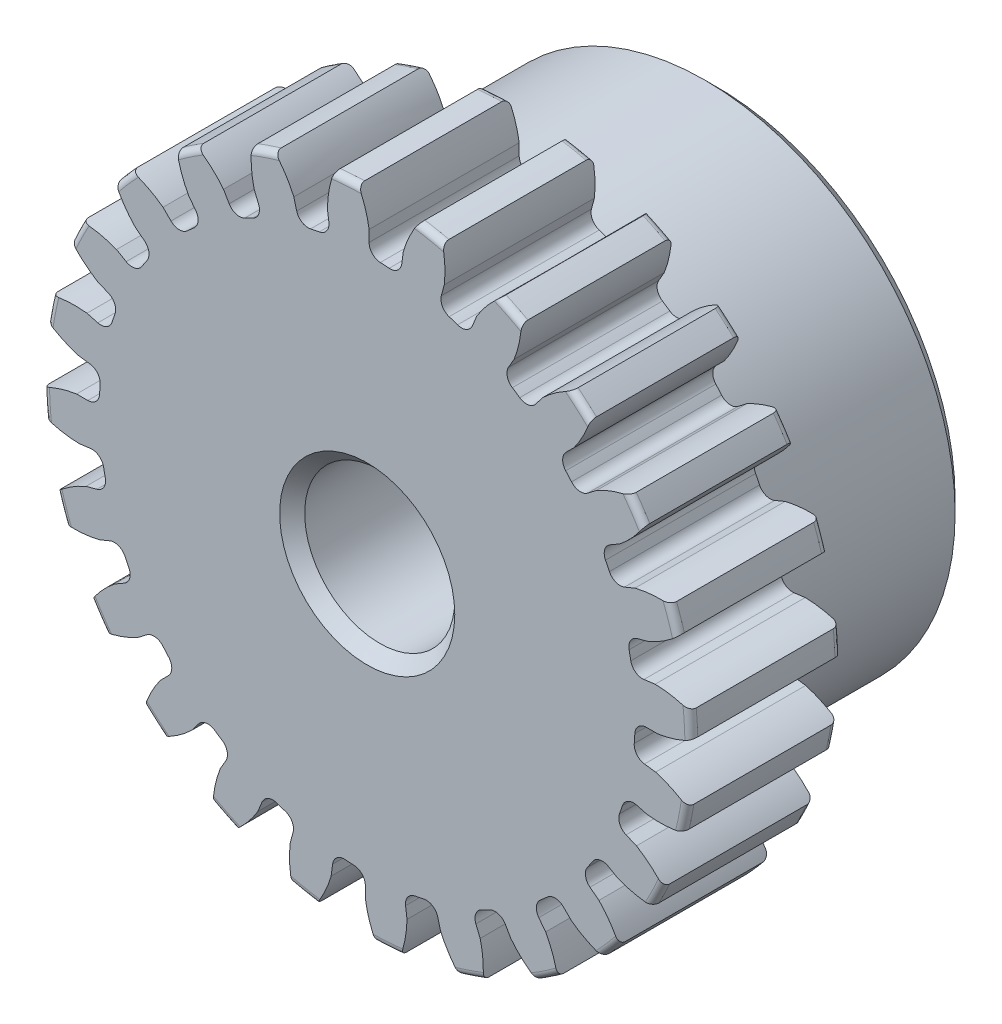
SolidWorks part; units mm, degrees
ref_plane "Front" through (0, 0, 0) normal (0, 0, 1) x (1, 0, 0)
ref_plane "Top" through (0, 0, 0) normal (0, 1, 0) x (1, 0, 0)
ref_plane "Right" through (0, 0, 0) normal (1, 0, 0) x (0, 0, -1)
sketch "Sketch1" plane through (0, 0, 0) normal (0, 0, 1) x (1, 0, 0)
  line L0 (-304.8, 0) -> (304.8, 0) construction
  circle A0 centre (0, 0) radius 10.287
  circle A1 centre (0, 0) radius 9.525 construction
  circle A3 centre (0, 0) radius 8.5011 construction
  dimension "D1" = 1.7859
  dimension "OD" = 20.574
  dimension "Ptich Dia" = 19.05
  dimension "Root Dia" = 17.0021
  dimension "D3" = 0.762
  dimension "Number of Teeth" = 609.6
extrude "Boss-Extrude1" add sketch "Sketch1" against normal blind 4.7625
sketch "Sketch2" plane through (0, 0, 0) normal (1, 0, 0) x (0, 0, -1)
  line L0 (4.7625, 0) -> (11.1125, 0)
  line L1 (4.7625, 0) -> (4.7625, 7.9375)
  line L2 (4.7625, 7.9375) -> (11.1125, 7.9375)
  line L3 (11.1125, 7.9375) -> (11.1125, 0)
  point P5 (11.1125, -7.9375)
  point P6 (0, -10.287)
  point P7 (4.7625, -10.287)
  point P9 (0, 10.287)
  dimension "Face Wd" = 4.7625
  dimension "B Hub Dia" = 15.875
  dimension "D O'all Lg." = 11.1125
revolve "Revolve1" add sketch "Sketch2" angle 360 about L0
fillet "Fillet2" radius 0.2057 3 edges at (10.287, 0, -4.7625) (10.287, 0, 0) (7.9375, 0, -4.7625)
sketch "Sketch3" plane through (0, 0, 0) normal (0, 0, 1) x (1, 0, 0)
  line L0 (0, 0) -> (0, 10.287) construction
  line L1 (-2.3089, 8.9279) -> (0, 9.525)
  line L2 (-9.5921, 9.525) -> (9.5921, 9.525) construction
  line L3 (-9.2865, 7.1233) -> (9.2865, 11.9267) construction
  line L4 (-2.3089, 8.9279) -> (0, 0) construction
  line L5 (-5.8892, 7.0961) -> (0, 0) construction
  line L6 (-5.8892, 7.0961) -> (-0.9538, 11.1922) construction
  line L7 (-1.61, 9.08) -> (0, 0) construction
  line L8 (-1.61, 9.08) -> (0.0338, 9.3714) construction
  arc A0 (-2.3089, 8.9279) -> (-5.8892, 7.0961) centre (0, 0) ccw
  circle A1 centre (0, 0) radius 9.525 construction
  circle A2 centre (0, 0) radius 9.2216 construction
  arc A3 (-2.3089, 8.9279) -> (-1.61, 9.08) centre (0, 0) cw
  circle A4 centre (0, 0) radius 10.287 construction
  point P6 (0, 9.525)
  dimension "D1" = 2.3849
  dimension "Pressure Angle" = 14.5
  dimension "D2" = 4.0543
  dimension "D3" = 6.4137
  dimension "D4" = 0.7155
  dimension "D5" = 1.6694
sketch "Sketch4" plane through (0, 0, 0) normal (0, 0, 1) x (1, 0, 0)
  line L0 (0, 0) -> (0.6216, 9.4843) construction
  line L1 (0.0598, 9.2214) -> (0.0598, 8.5009)
  line L2 (0, 9.525) -> (1.2433, 9.4435) construction
  line L3 (1.1444, 9.1503) -> (1.0503, 8.4359)
  line L4 (0.0598, 8.5009) -> (0, 0) construction
  line L5 (0, 0) -> (0, 10.287) construction
  line L6 (-5.8892, 7.0961) -> (-0.9538, 11.1922) construction
  line L7 (-5.8892, 7.0961) -> (-0.9538, 11.1922) construction
  arc A0 (1.0503, 8.4359) -> (0.0598, 8.5009) centre (0, 0) ccw
  arc A1 (0, 9.525) -> (1.2433, 9.4435) centre (0, 0) cw construction
  circle A2 centre (0, 0) radius 9.525 construction
  circle A3 centre (0, 0) radius 9.2216 construction
  circle A4 centre (0, 0) radius 8.5011 construction
  arc A5 (2.4065, 10.9719) -> (-0.9538, 11.1922) centre (0, 0) ccw
  spline S0 degree 2 poles (-0.9538, 11.1922) (-0.1068, 10.325) (0.0598, 9.2214) knots 0 0 0 1 1 1
  spline S1 degree 2 poles (2.4065, 10.9719) (1.4536, 10.2227) (1.1444, 9.1503) knots 0 0 0 1 1 1
  dimension "D1" = 1.2468
extrude "Cut-Extrude1" cut sketch "Sketch4" against normal through all
fillet "Fillet1" radius 0.374 2 edges at (1.0503, 8.4359, -2.3813) (0.0598, 8.5009, -2.3813)
pattern_circular "CirPattern1" count 24 over 360 about axis through (0, 0, -4.7625) along (0, 0, 1) of "Cut-Extrude1", "Fillet1"
sketch "Sketch5" plane through (0, 0, 0) normal (0, 0, 1) x (1, 0, 0)
  circle A0 centre (0, 0) radius 2.3813
  circle A1 centre (0, 0) radius 1.5875 construction
  dimension "Bore Min" = 4.7625
  dimension "Bore Max" = 3.175
extrude "Cut-Extrude2" cut sketch "Sketch5" against normal through all
chamfer "Chamfer1" distance 0.3969 angle 45 3 edges at (7.9375, 0, -11.1125) (2.3813, 0, 0) (2.3813, 0, -11.1125)
sketch "Pitch Dia" plane through (0, 0, 0) normal (0, 0, 1) x (1, 0, 0)
  circle A0 centre (0, 0) radius 9.525 construction
  circle A1 centre (0, 0) radius 9.525 construction
equation "\"D1@Boss-Extrude1\" = \"Face Wd@Sketch2\""
equation "\"D2@Sketch3\" = \"D1@Sketch3\"*1.7"
equation "\"D3@Sketch3\" = \"D1@Sketch3\"+\"D2@Sketch3\"-.001"
equation "\"D4@Sketch3\" = \"D1@Sketch3\"*.3"
equation "\"D5@Sketch3\" = \"D1@Sketch3\"-\"D4@Sketch3\""
equation "\"D1@Sketch4\" = 1.5708/(\"Number of Teeth@Sketch1\"/\"Ptich Dia@Sketch1\")"
equation "\"D1@Chamfer1\" = \"B Hub Dia@Sketch2\"*.025"
equation "\"D1@CirPattern1\" = \"Number of Teeth@Sketch1\""
equation "\"D1@Fillet1\" = \"D1@Sketch4\"*.3"
equation "\"D1@Fillet2\" = \"OD@Sketch1\"*.01"
equation "\"D1@Sketch1\" = 2.250/(\"Number of Teeth@Sketch1\"/\"Ptich Dia@Sketch1\")"
